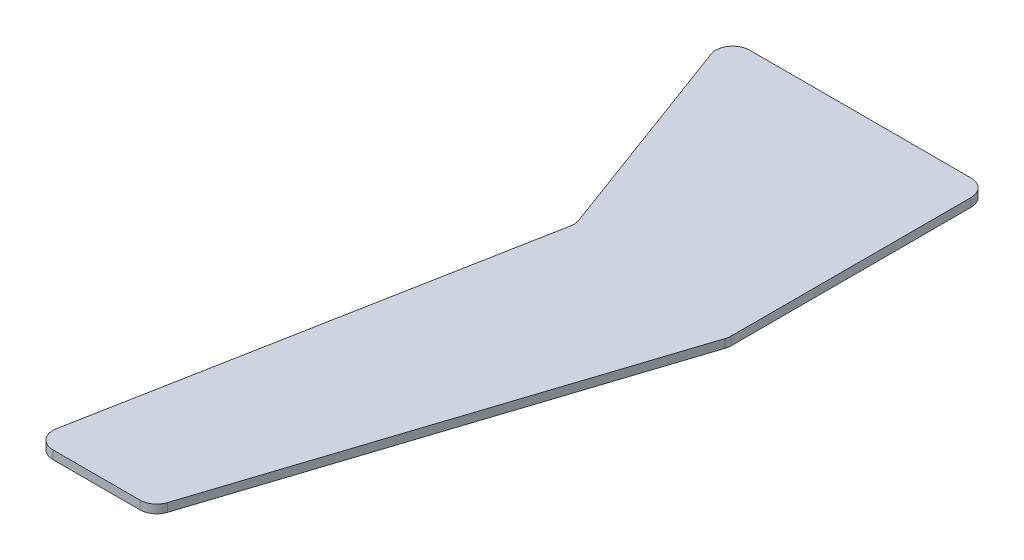
SolidWorks part; units mm, degrees
ref_plane "Front Plane" through (0, 0, 0) normal (0, 0, 1) x (1, 0, 0)
ref_plane "Top Plane" through (0, 0, 0) normal (0, 1, 0) x (1, 0, 0)
ref_plane "Right Plane" through (0, 0, 0) normal (1, 0, 0) x (0, 0, -1)
sketch "Sketch1" plane through (0, 0, 0) normal (0, 1, 0) x (1, 0, 0)
  line L0 (-37.6966, -112.1663) -> (-18.4697, -10.0199)
  line L1 (-13.2776, -116.9062) -> (-33.7657, -116.9062)
  line L2 (22.8066, -14.7947) -> (-9.4734, -114.1423)
  line L3 (23.0024, 43.0579) -> (23.0024, -13.5586)
  line L4 (-33.2509, 47.0579) -> (19.0024, 47.0579)
  line L5 (-18.6496, -7.891) -> (-37.002, 41.6688)
  arc A0 (-37.6966, -112.1663) -> (-33.7657, -116.9062) centre (-33.7657, -112.9062) ccw
  arc A1 (-13.2776, -116.9062) -> (-9.4734, -114.1423) centre (-13.2776, -112.9062) ccw
  arc A2 (22.8066, -14.7947) -> (23.0024, -13.5586) centre (19.0024, -13.5586) ccw
  arc A3 (23.0024, 43.0579) -> (19.0024, 47.0579) centre (19.0024, 43.0579) ccw
  arc A4 (-33.2509, 47.0579) -> (-37.002, 41.6688) centre (-33.2509, 43.0579) ccw
  arc A5 (-18.4697, -10.0199) -> (-18.6496, -7.891) centre (-22.4007, -9.28) ccw
  point P0 (0, 0)
extrude "Boss-Extrude1" add sketch "Sketch1" along normal blind 2
